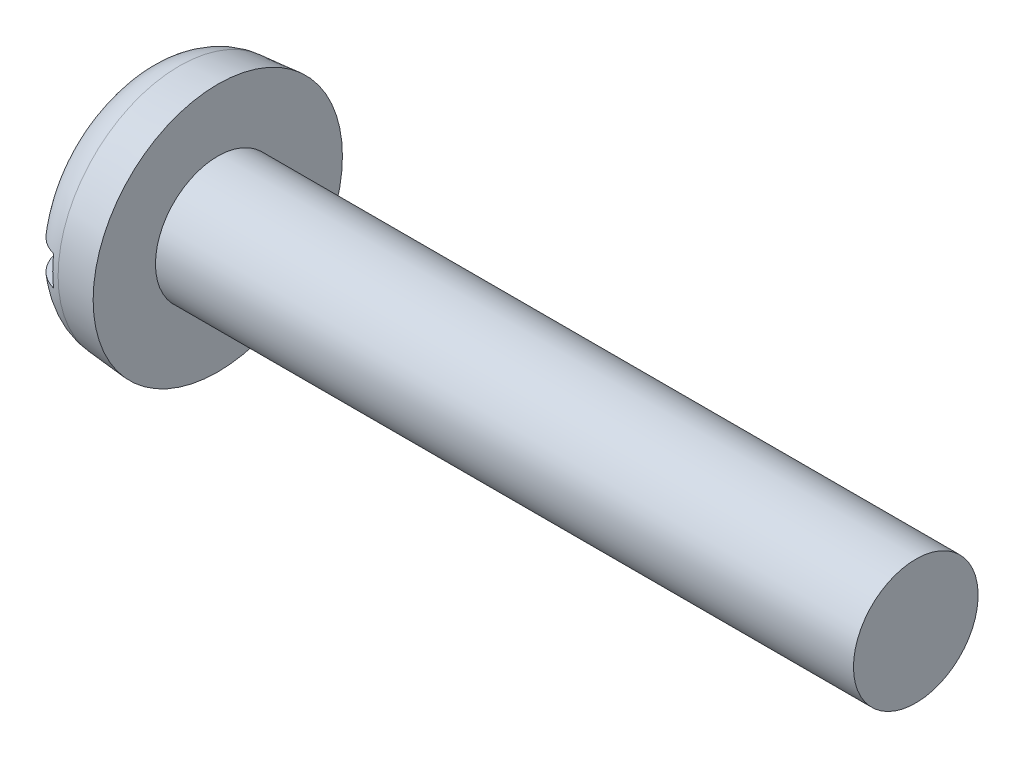
SolidWorks part; units mm, degrees
ref_plane "Plane1" through (0, 0, 0) normal (0, 0, 1) x (1, 0, 0)
ref_plane "Plane2" through (0, 0, 0) normal (0, 1, 0) x (1, 0, 0)
ref_plane "Plane3" through (0, 0, 0) normal (1, 0, 0) x (0, 0, -1)
sketch "BodySke" plane through (0, 0, 0) normal (0, 0, 1) x (1, 0, 0)
  line L0 (1.5, 1.25) -> (1.5, 2.5)
  line L1 (0, 0) -> (0, 2.3688)
  line L2 (-25.4, 0) -> (127, 0) construction
  line L3 (15.5, 0) -> (0, 0)
  line L4 (1.5, 1.25) -> (15.5, 1.25)
  line L5 (15.5, 1.25) -> (15.5, 0)
  line L6 (0, 2.3688) -> (1.5, 2.5)
  line L9 (1.95, 2.8375) -> (1.95, -6.6875) construction
  line L10 (1.5, 6.35) -> (1.5, -3.175) construction
  dimension "Length" = 14
  dimension "Head_ht" = 1.5
  dimension "Advance" = 0.45
  dimension "Thread_nom" = 14
  dimension "Head_dia" = 5
  dimension "Head_side_angle" = 5
  dimension "Diameter" = 2.5
revolve "Base-Revolve" add sketch "BodySke"
cosmetic thread "ThreadCosmetic" [suppressed]
fillet "Fillet1" [suppressed] radius 0.1
fillet "Fillet2" radius 0.8 1 edges at (0, 0, 2.3688)
sketch "Sketch2" plane through (0, 0, 0) normal (1, 0, 0) x (0, 0, -1)
  line L0 (2.5, -0.3) -> (-2.5, -0.3)
  line L1 (2.5, -0.3) -> (2.5, 0.3)
  line L2 (-2.5, 0.3) -> (2.5, 0.3)
  line L3 (-2.5, 0.3) -> (-2.5, -0.3)
  dimension "D1" = 5
  dimension "Slot_width" = 0.6
  dimension "D2" = 2.5
  dimension "D3" = 0.3
extrude "Slot" cut sketch "Sketch2" along normal blind 0.6
sketch "ThdSchSke" plane through (0, 0, 0) normal (0, 0, 1) x (1, 0, 0)
  line L0 (2.4, -0.9965) -> (2.2225, -1.25)
  line L1 (2.4, -0.9965) -> (2.5775, -1.25)
  line L2 (2.5775, -1.25) -> (2.5775, -1.5625)
  line L3 (-3.175, 0) -> (5.1513, 0) construction
  line L5 (2.5775, -1.5625) -> (2.2225, -1.5625)
  line L6 (2.2225, -1.5625) -> (2.2225, -1.25)
  dimension "Diameter" = 2.5
  dimension "SideAngle" = 55
  dimension "VeeAngle" = 70
  dimension "Thread_minor" = 1.993
  dimension "Overcut" = 3.125
  dimension "Start" = 2.4
revolve "ThreadSchematic" [suppressed] cut sketch "ThdSchSke" angle 360 about L3
pattern_linear "ThdSchPat" [suppressed]
equation "\"D1@Sketch2\" = \"Head_dia@BodySke\""
equation "\"D2@Sketch2\" = \"D1@Sketch2\" / 2"
equation "\"D3@Sketch2\" = \"Slot_width@Sketch2\" / 2"
equation "\"Thread_length@ThreadCosmetic\" = ((sgn( (\"Length@BodySke\" - \"Advance@BodySke\" * 2.0 ) - \"Thread_nom@BodySke\" )-1)*( (\"Length@BodySke\" - \"Advance@BodySke\"  * 2.0) - \"Thread_nom@BodySke\" ))/-2+ \"Thread_nom@BodySke\""
equation "\"Thread_minor@ThdSchSke\" = \"Thread_minor@ThreadCosmetic\""
equation "\"Diameter@ThdSchSke\" = \"Diameter@BodySke\""
equation "\"Overcut@ThdSchSke\" = \"Diameter@BodySke\" * 1.25"
equation "\"Start@ThdSchSke\" = \"Head_ht@BodySke\" + \"Length@BodySke\" - \"Thread_length@ThreadCosmetic\"  '---Non-countersunk---"
equation "\"Num_threads@ThdSchPat\" = int( \"Thread_length@ThreadCosmetic\" / \"Advance@BodySke\" + 0.999 )  + 1"
equation "\"Advance@ThdSchPat\" = \"Thread_length@ThreadCosmetic\" /  (\"Num_threads@ThdSchPat\" - 1) 'relax it"
